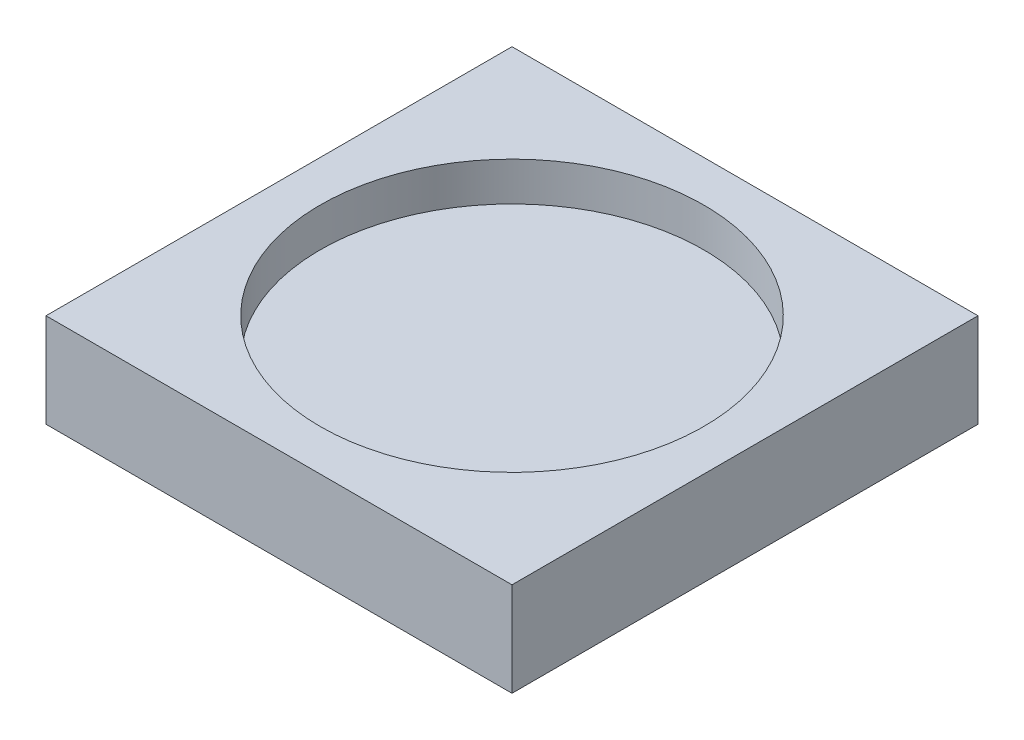
SolidWorks part; units mm, degrees
ref_plane "Front Plane" through (0, 0, 0) normal (0, 0, 1) x (1, 0, 0)
ref_plane "Top Plane" through (0, 0, 0) normal (0, 1, 0) x (1, 0, 0)
ref_plane "Right Plane" through (0, 0, 0) normal (1, 0, 0) x (0, 0, -1)
sketch "Sketch1" plane through (0, 0, 0) normal (0, 1, 0) x (1, 0, 0)
  line L1 (0, 0) -> (152.4, 0)
  line L2 (0, 0) -> (0, 152.4)
  line L3 (0, 152.4) -> (152.4, 152.4)
  line L4 (152.4, 0) -> (152.4, 152.4)
  dimension "D1" = 152.4
  dimension "D2" = 152.4
extrude "Boss-Extrude1" add sketch "Sketch1" along normal blind 30.734
sketch "Sketch2" plane through (0, 30.734, 0) normal (0, 1, 0) x (1, 0, 0)
  line L4 (0, 76.2) -> (152.4, 76.2) construction
  line L5 (76.2, 0) -> (76.2, 152.4) construction
  line L6 (152.4, 152.4) -> (0, 152.4) construction
  line L7 (152.4, 0) -> (152.4, 152.4) construction
  line L8 (0, 152.4) -> (0, 0) construction
  line L9 (0, 0) -> (152.4, 0) construction
  circle A0 centre (76.2, 76.2) radius 62.738
  point P6 (0, 0)
  point P9 (0, 0)
  point P12 (0, 0)
  point P15 (0, 0)
  point P18 (76.2, 76.2)
  dimension "D1" = 125.476
extrude "Cut-Extrude1" cut sketch "Sketch2" against normal blind 12.7
